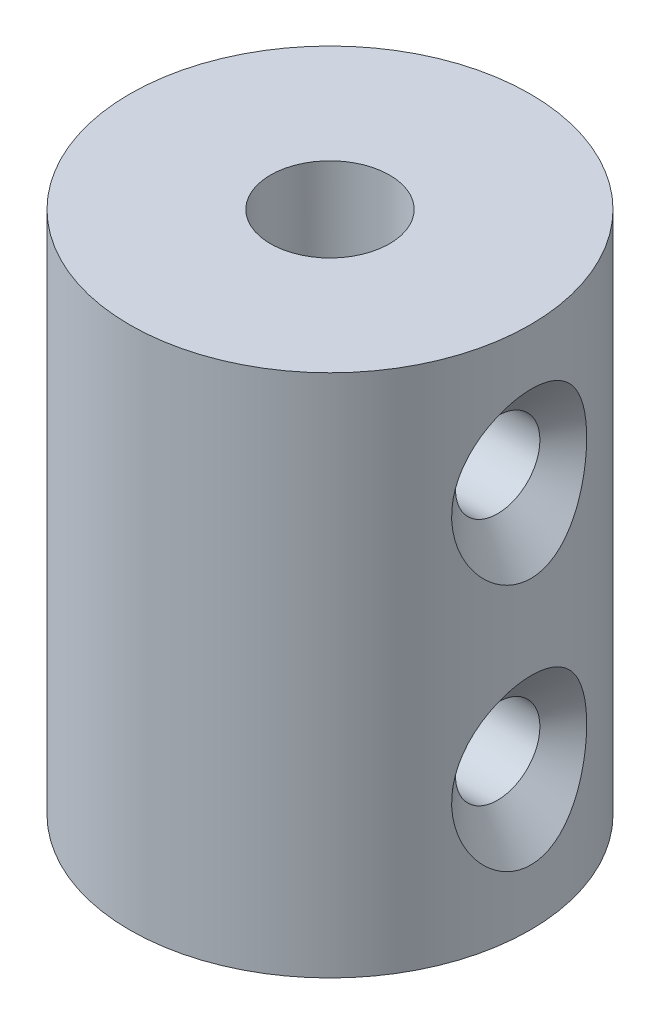
SolidWorks part; units mm, degrees
ref_plane "Front Plane" through (0, 0, 0) normal (0, 0, 1) x (1, 0, 0)
ref_plane "Top Plane" through (0, 0, 0) normal (0, 1, 0) x (1, 0, 0)
ref_plane "Right Plane" through (0, 0, 0) normal (1, 0, 0) x (0, 0, -1)
sketch "Sketch1" plane through (0, 0, 0) normal (0, 1, 0) x (1, 0, 0)
  circle A0 centre (0, 0) radius 5.334
extrude "Boss-Extrude1" add sketch "Sketch1" along normal blind 13.97
sketch "Sketch2" plane through (0, 0, 0) normal (0, -1, 0) x (-1, 0, 0)
  circle A0 centre (0, 0) radius 1.5875
extrude "Cut-Extrude1" cut sketch "Sketch2" against normal through all
ref_plane "Plane1" through (5.334, 0, 0) normal (1, 0, 0) x (0, 0, -1)
sketch "Sketch3" plane through (5.334, 0, 0) normal (1, 0, 0) x (0, 0, -1)
  line L0 (0, 0) -> (0, 3.302) construction
  dimension "D1" = 3.302
hole_wizard "CSK for #2 Flat Head Machine Screw (100)2" positions "3DSketch3" profile "Sketch6" countersink size "#2" standard "ANSI Inch"
sketch3d "3DSketch3"
  point P0 (5.334, 3.302, 0)
  point P3 (5.334, 3.302, 0)
  point P5 (5.3339, 3.6791, -0.0244)
sketch "Sketch6" plane through (5.3339, 3.6791, -0.0244) normal (0, 1, 0) x (-0.0046, 0, -1)
  line L0 (0, 0) -> (0, 7.5372)
  line L1 (0, 7.5372) -> (1.1303, 6.858)
  line L2 (1.1303, 6.858) -> (1.1303, 0.8845)
  line L3 (1.1303, 0.8845) -> (2.1844, 0)
  line L5 (2.1844, 0) -> (0, 0)
  line L6 (-1.1303, 0.8845) -> (-2.1844, 0) construction
  line L10 (0, 7.5372) -> (-1.1303, 6.858) construction
  line L11 (0, -6.35) -> (0, 107.95) construction
  dimension "Hole Dia." = 2.2606
  dimension "Hole Depth" = 6.858
  dimension "Near C'Sink Dia." = 4.3688
  dimension "Near C'Sink Angle" = 100
  dimension "Drill Angle" = 118
ref_plane "Plane3" through (0, 6.985, 0) normal (0, -1, 0) x (-1, 0, 0)
mirror "Mirror3" about plane through (0, 6.985, 0) normal (0, -1, 0) of "CSK for #2 Flat Head Machine Screw (100)2"
